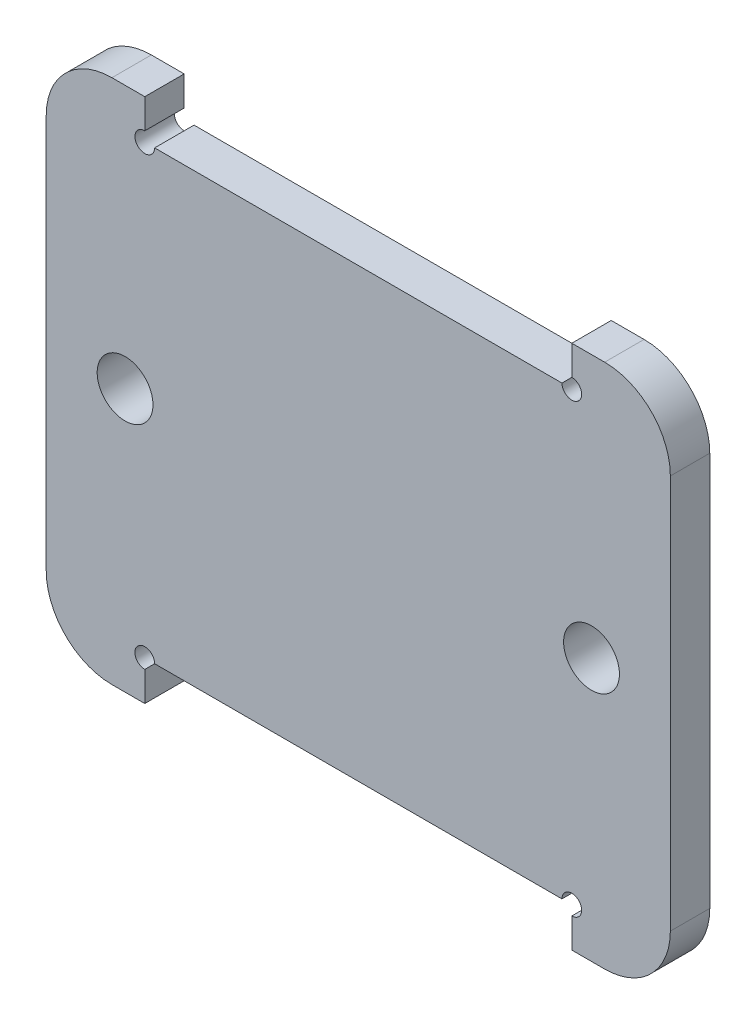
SolidWorks part; units mm, degrees
material "1.0553 (S355J0)"
ref_plane "Front Plane" through (0, 0, 0) normal (0, 0, 1) x (1, 0, 0)
ref_plane "Top Plane" through (0, 0, 0) normal (0, 1, 0) x (1, 0, 0)
ref_plane "Right Plane" through (0, 0, 0) normal (1, 0, 0) x (0, 0, -1)
sketch "Sketch1" plane through (0, 0, 0) normal (0, 0, 1) x (1, 0, 0)
  line L0 (-347.5, 26) -> (-347.5, 94) construction
  line L1 (-330.5, 26) -> (-364.5, 26) construction
  line L2 (-364.5, 94) -> (-330.5, 94) construction
  line L3 (-380, 94) -> (-315, 94)
  line L4 (-315, 94) -> (-315, 100)
  line L6 (-315, 100) -> (-310, 100)
  line L7 (-300, 90) -> (-300, 30)
  line L8 (-310, 20) -> (-315, 20)
  line L9 (-315, 20) -> (-315, 26)
  line L10 (-325.5, 26) -> (-330.5, 26) construction
  line L12 (-315, 26) -> (-380, 26)
  line L13 (-300, 60) -> (-395, 60) construction
  line L14 (-380, 20) -> (-380, 26)
  line L15 (-385, 20) -> (-380, 20)
  line L16 (-395, 90) -> (-395, 30)
  line L17 (-380, 100) -> (-385, 100)
  line L18 (-380, 94) -> (-380, 100)
  line L19 (-315, 26) -> (-315, 20) construction
  line L20 (-325.5, 20) -> (-315, 20) construction
  line L21 (-315, 100) -> (-315, 94) construction
  arc A0 (-310, 100) -> (-300, 90) centre (-310, 90) cw
  arc A1 (-300, 30) -> (-310, 20) centre (-310, 30) cw
  circle A2 centre (-312, 60) radius 4.25
  circle A3 centre (-383, 60) radius 4.25
  arc A4 (-395, 30) -> (-385, 20) centre (-385, 30) ccw
  arc A5 (-385, 100) -> (-395, 90) centre (-385, 90) ccw
  point P29 (-347.5, 60)
  dimension "D1" = 10
  dimension "D2" = 8.5
  dimension "D3" = 5
  dimension "D4" = 12
extrude "Boss-Extrude1" add sketch "Sketch1" along normal blind 6
sketch "Sketch2" plane through (0, 0, 6) normal (0, 0, 1) x (1, 0, 0)
  line L0 (-347.5, 26) -> (-347.5, 94) construction
  line L1 (-380, 26) -> (-315, 26) construction
  line L2 (-315, 94) -> (-380, 94) construction
  line L3 (-300, 60) -> (-395, 60) construction
  line L4 (-300, 30) -> (-300, 90) construction
  line L5 (-395, 90) -> (-395, 30) construction
  circle A0 centre (-380, 26) radius 1.5
  circle A1 centre (-315, 26) radius 1.5
  circle A2 centre (-380, 94) radius 1.5
  circle A3 centre (-315, 94) radius 1.5
  dimension "D1" = 3
extrude "Cut-Extrude1" cut sketch "Sketch2" against normal through all
ref_plane "Plane1" through (-347.5, 0, 0) normal (1, 0, 0) x (0, 0, -1)
